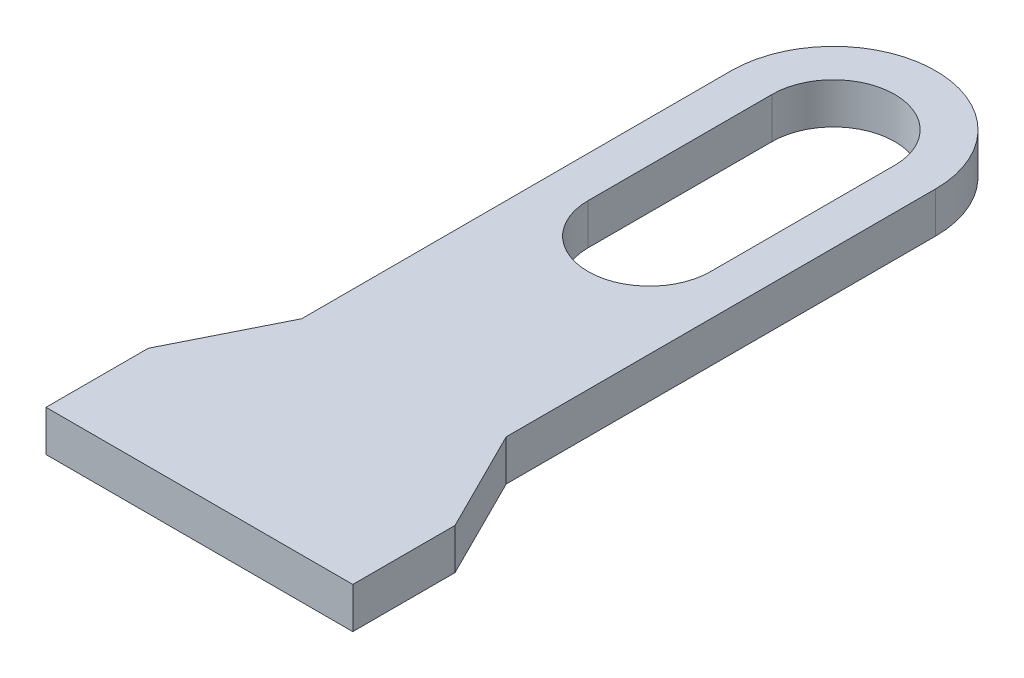
SolidWorks part; units mm, degrees
ref_plane "Front Plane" through (0, 0, 0) normal (0, 0, 1) x (1, 0, 0)
ref_plane "Top Plane" through (0, 0, 0) normal (0, 1, 0) x (1, 0, 0)
ref_plane "Right Plane" through (0, 0, 0) normal (1, 0, 0) x (0, 0, -1)
sketch "Sketch1" plane through (0, 0, 0) normal (0, 1, 0) x (1, 0, 0)
  line L0 (1.5, 0) -> (-1.5, 0)
  line L1 (-1.5, 0) -> (-1.5, 1)
  line L2 (-1.5, 1) -> (-1, 2)
  line L3 (-1, 2) -> (-1, 6.2)
  line L4 (0, 0) -> (0, 6.2)
  line L5 (0, 4.4) -> (0, 6.2) construction
  line L6 (-0.6, 4.4) -> (-0.6, 6.2)
  line L7 (0.6, 4.4) -> (0.6, 6.2)
  line L8 (1.5, 0) -> (1.5, 1)
  line L9 (1.5, 1) -> (1, 2)
  line L10 (1, 2) -> (1, 6.2)
  arc A0 (-1, 6.2) -> (1, 6.2) centre (0, 6.2) cw
  arc A1 (-0.6, 4.4) -> (0.6, 4.4) centre (0, 4.4) ccw
  arc A2 (0.6, 6.2) -> (-0.6, 6.2) centre (0, 6.2) ccw
  point P9 (0, 5.3)
  point P19 (0, 3.8)
  point P21 (0, 6.8)
  dimension "D6" = 0.6
  dimension "D1" = 2
  dimension "D2" = 6.2
  dimension "D3" = 3
  dimension "D4" = 1
  dimension "D5" = 2
  dimension "D7" = 3
extrude "Boss-Extrude1" add sketch "Sketch1" along normal blind 0.4
